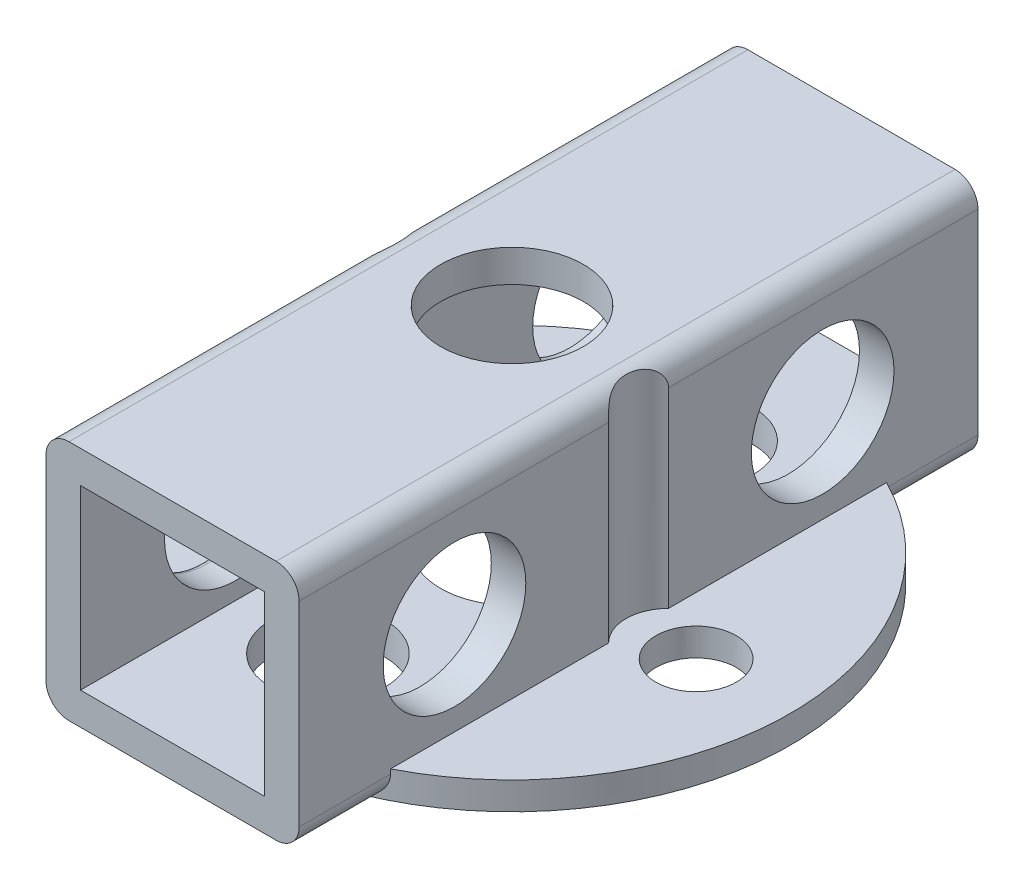
SolidWorks part; units mm, degrees
material "ABS"
ref_plane "Front Plane" through (0, 0, 0) normal (0, 0, 1) x (1, 0, 0)
ref_plane "Top Plane" through (0, 0, 0) normal (0, 1, 0) x (1, 0, 0)
ref_plane "Right Plane" through (0, 0, 0) normal (1, 0, 0) x (0, 0, -1)
ref_plane "Plane1" through (0, 0, 0) normal (0, -1, 0) x (1, 0, 0)
sketch "Sketch1" plane through (0, 0, 0) normal (0, -1, 0) x (1, 0, 0)
  line L0 (-5.5, 14.75) -> (-5.5, -14.75)
  line L1 (-5.5, -14.75) -> (5.5, -14.75)
  line L2 (5.5, -14.75) -> (5.5, 14.75)
  line L3 (5.5, 14.75) -> (-5.5, 14.75)
extrude "Boss-Extrude1" add sketch "Sketch1" against normal blind 10.5
sketch "Sketch2" plane through (0, 0, 0) normal (0, -1, 0) x (1, 0, 0)
  line L0 (-5.5, -10.7778) -> (-5.5, 10.7778)
  arc A0 (-5.5, 10.7778) -> (-5.5, -10.7778) centre (0, 0) ccw
extrude "Boss-Extrude2" add sketch "Sketch2" against normal blind 1.2
sketch "Sketch3" plane through (0, 10.5, 0) normal (0, 1, 0) x (-1, 0, 0)
  line L0 (5.5, -1.3022) -> (5.5, 1.3022)
  arc A0 (5.5, 1.3022) -> (5.5, -1.3022) centre (6.8, 0) ccw
extrude "Cut-Extrude1" cut sketch "Sketch3" against normal blind 9.3
sketch "Sketch4" plane through (0, 0, 0) normal (0, -1, 0) x (1, 0, 0)
  line L0 (5.5, 10.7778) -> (5.5, -10.7778)
  arc A0 (5.5, -10.7778) -> (5.5, 10.7778) centre (0, 0) ccw
extrude "Boss-Extrude3" add sketch "Sketch4" against normal blind 1.2
sketch "Sketch5" plane through (0, 10.5, 0) normal (0, 1, 0) x (-1, 0, 0)
  line L0 (-5.5, 1.3022) -> (-5.5, -1.3022)
  arc A0 (-5.5, -1.3022) -> (-5.5, 1.3022) centre (-6.8, 0) ccw
extrude "Cut-Extrude2" cut sketch "Sketch5" against normal blind 9.3
sketch "Sketch6" plane through (0, 0, 14.75) normal (0, 0, 1) x (1, 0, 0)
  line L0 (-4, 9.1) -> (-4, 1.4)
  line L1 (-4, 1.4) -> (4, 1.4)
  line L2 (4, 1.4) -> (4, 9.1)
  line L3 (4, 9.1) -> (-4, 9.1)
extrude "Cut-Extrude3" cut sketch "Sketch6" against normal through all
hole_wizard "Ø5.0 (5) Diameter Hole1" positions "Sketch8" profile "Sketch7" hole size "Ø5.0" standard "ANSI Metric"
sketch "Sketch8" plane through (0, 0, 0) normal (0, -1, 0) x (-1, 0, 0)
  point P0 (0, -8)
sketch "Sketch7" plane through (0, 0, 8) normal (1, 0, 0) x (0, 0, -1)
  line L0 (0, 0) -> (0, 1.4)
  line L1 (0, 1.4) -> (2.5, 1.4)
  line L2 (2.5, 1.4) -> (2.5, 0)
  line L5 (2.5, 0) -> (0, 0)
  line L11 (0, -6.35) -> (0, 107.95) construction
  dimension "Thru Hole Dia." = 5
  dimension "Thru Hole Depth" = 1.4
hole_wizard "Ø5.0 (5) Diameter Hole2" positions "Sketch10" profile "Sketch9" hole size "Ø5.0" standard "ANSI Metric"
sketch "Sketch10" plane through (0, 0, 0) normal (0, -1, 0) x (-1, 0, 0)
  point P0 (0, 8)
sketch "Sketch9" plane through (0, 0, -8) normal (1, 0, 0) x (0, 0, -1)
  line L0 (0, 0) -> (0, 1.4)
  line L1 (0, 1.4) -> (2.5, 1.4)
  line L2 (2.5, 1.4) -> (2.5, 0)
  line L5 (2.5, 0) -> (0, 0)
  line L11 (0, -6.35) -> (0, 107.95) construction
  dimension "Thru Hole Dia." = 5
  dimension "Thru Hole Depth" = 1.4
ref_plane "Plane2" through (0, 0, -8) normal (0, 0, -1) x (-1, 0, 0)
sketch "Sketch11" plane through (0, 0, -8) normal (0, 0, -1) x (-1, 0, 0)
  line L0 (-1.6, -0.75) -> (0, -0.75)
  line L1 (0, -0.75) -> (0, 0.25)
  line L2 (0, 0.25) -> (-1.6, 0.25)
  line L3 (-1.6, 0.25) -> (-1.6, -0.75)
  line L4 (0, -0.75) -> (0, 0.25) construction
revolve "Revolve1" add sketch "Sketch11" angle 360 about L4
ref_plane "Plane3" through (0, 0, 8) normal (0, 0, -1) x (-1, 0, 0)
sketch "Sketch12" plane through (0, 0, 8) normal (0, 0, -1) x (-1, 0, 0)
  line L0 (-1.6, -0.75) -> (0, -0.75)
  line L1 (0, -0.75) -> (0, 0.25)
  line L2 (0, 0.25) -> (-1.6, 0.25)
  line L3 (-1.6, 0.25) -> (-1.6, -0.75)
  line L4 (0, -0.75) -> (0, 0.25) construction
revolve "Revolve2" add sketch "Sketch12" angle 360 about L4
hole_wizard "Ø6.2 (6.2) Diameter Hole1" positions "Sketch14" profile "Sketch13" hole size "Ø6.2" standard "ANSI Metric"
sketch "Sketch14" plane through (0, 0, 0) normal (0, -1, 0) x (-1, 0, 0)
  point P0 (0, 0)
sketch "Sketch13" plane through (0, 0, 0) normal (1, 0, 0) x (0, 0, -1)
  line L0 (0, 0) -> (0, 1.4)
  line L1 (0, 1.4) -> (3.1, 1.4)
  line L2 (3.1, 1.4) -> (3.1, 0)
  line L5 (3.1, 0) -> (0, 0)
  line L11 (0, -6.35) -> (0, 107.95) construction
  dimension "Thru Hole Dia." = 6.2
  dimension "Thru Hole Depth" = 1.4
hole_wizard "Ø3.5 (3.5) Diameter Hole1" positions "Sketch16" profile "Sketch15" hole size "Ø3.5" standard "ANSI Metric"
sketch "Sketch16" plane through (0, 1.2, 0) normal (0, 1, 0) x (1, 0, 0)
  point P0 (8, 0)
  point P1 (-8, 0)
sketch "Sketch15" plane through (8, 1.2, 0) normal (1, 0, 0) x (0, 0, 1)
  line L0 (0, 0) -> (0, 1.2)
  line L1 (0, 1.2) -> (1.75, 1.2)
  line L2 (1.75, 1.2) -> (1.75, 0)
  line L5 (1.75, 0) -> (0, 0)
  line L11 (0, -6.35) -> (0, 107.95) construction
  dimension "Thru Hole Dia." = 3.5
  dimension "Thru Hole Depth" = 1.2
hole_wizard "Ø6.2 (6.2) Diameter Hole2" positions "Sketch18" profile "Sketch17" hole size "Ø6.2" standard "ANSI Metric"
sketch "Sketch18" plane through (5.5, 0, 0) normal (1, 0, 0) x (0, 0, -1)
  point P0 (-8, 5.25)
  point P1 (8, 5.25)
sketch "Sketch17" plane through (5.5, 5.25, 8) normal (0, 1, 0) x (0, 0, -1)
  line L0 (0, 0) -> (0, 1.5)
  line L1 (0, 1.5) -> (3.1, 1.5)
  line L2 (3.1, 1.5) -> (3.1, 0)
  line L5 (3.1, 0) -> (0, 0)
  line L11 (0, -6.35) -> (0, 107.95) construction
  dimension "Thru Hole Dia." = 6.2
  dimension "Thru Hole Depth" = 1.5
hole_wizard "Ø6.2 (6.2) Diameter Hole3" positions "Sketch20" profile "Sketch19" hole size "Ø6.2" standard "ANSI Metric"
sketch "Sketch20" plane through (-5.5, 0, 0) normal (-1, 0, 0) x (0, 0, 1)
  point P0 (8, 5.25)
  point P1 (-8, 5.25)
sketch "Sketch19" plane through (-5.5, 5.25, 8) normal (0, 1, 0) x (0, 0, 1)
  line L0 (0, 0) -> (0, 1.5)
  line L1 (0, 1.5) -> (3.1, 1.5)
  line L2 (3.1, 1.5) -> (3.1, 0)
  line L5 (3.1, 0) -> (0, 0)
  line L11 (0, -6.35) -> (0, 107.95) construction
  dimension "Thru Hole Dia." = 6.2
  dimension "Thru Hole Depth" = 1.5
hole_wizard "Ø6.2 (6.2) Diameter Hole4" positions "Sketch22" profile "Sketch21" hole size "Ø6.2" standard "ANSI Metric"
sketch "Sketch22" plane through (0, 10.5, 0) normal (0, 1, 0) x (1, 0, 0)
  point P0 (0, 0)
sketch "Sketch21" plane through (0, 10.5, 0) normal (1, 0, 0) x (0, 0, 1)
  line L0 (0, 0) -> (0, 1.4)
  line L1 (0, 1.4) -> (3.1, 1.4)
  line L2 (3.1, 1.4) -> (3.1, 0)
  line L5 (3.1, 0) -> (0, 0)
  line L11 (0, -6.35) -> (0, 107.95) construction
  dimension "Thru Hole Dia." = 6.2
  dimension "Thru Hole Depth" = 1.4
ref_plane "Plane4" through (0, 0, 4) normal (0, 0, -1) x (-1, 0, 0)
sketch "Sketch23" plane through (0, 0, 4) normal (0, 0, -1) x (-1, 0, 0)
  line L0 (-5.5, 8.2) -> (-9.5, 1.2)
ref_plane "Plane5" through (0, 0, -4) normal (0, 0, 1) x (1, 0, 0)
sketch "Sketch24" plane through (0, 0, -4) normal (0, 0, 1) x (1, 0, 0)
  line L0 (-5.5, 8.2) -> (-9.5, 1.2)
ref_plane "Plane6" through (0, 0, 4) normal (0, 0, 1) x (1, 0, 0)
fillet "Fillet1" radius 1 6 edges at (5.5, 0, -12.7639) (-5.5, 0, 12.7639) (-5.5, 0, -12.7639) (5.5, 10.5, 8.0261) (5.5, 0, 12.7639) (-5.5, 10.5, -8.0261)
fillet "Fillet3" radius 0.25 1 edges at (-5.5, 5.25, 11.1)
